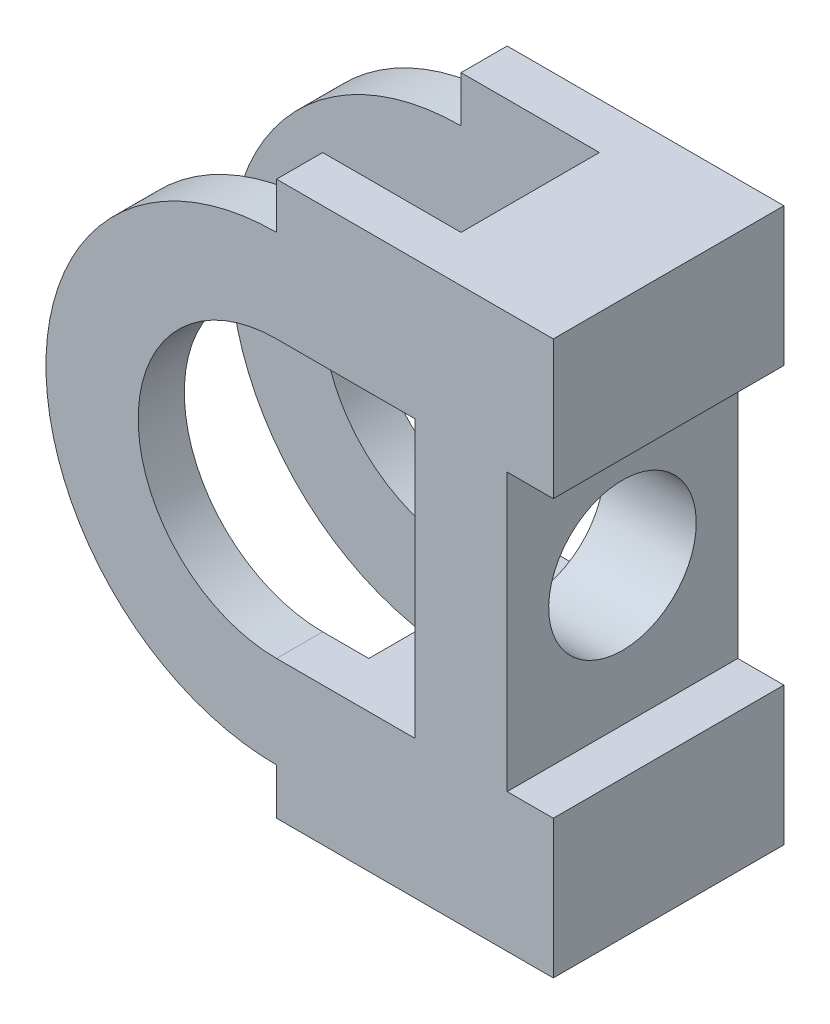
SolidWorks part; units mm, degrees
ref_plane "Front Plane" through (0, 0, 0) normal (0, 0, 1) x (1, 0, 0)
ref_plane "Top Plane" through (0, 0, 0) normal (0, 1, 0) x (1, 0, 0)
ref_plane "Right Plane" through (0, 0, 0) normal (1, 0, 0) x (0, 0, -1)
sketch "Sketch1" plane through (0, 0, 0) normal (0, 0, 1) x (1, 0, 0)
  line L0 (0, 120) -> (0, 110)
  line L1 (0, 0) -> (60, 0)
  line L2 (0, 0) -> (0, 10)
  line L3 (0, 120) -> (60, 120)
  line L4 (60, 0) -> (60, 120)
  arc A0 (0, 110) -> (0, 10) centre (0, 60) ccw
  dimension "D1" = 60
  dimension "D6" = 50
  dimension "D2" = 60
  dimension "D3" = 120
  dimension "D4" = 10
  dimension "D5" = 10
extrude "Boss-Extrude1" add sketch "Sketch1" along normal blind 50
sketch "Sketch2" plane through (0, 0, 50) normal (0, 0, 1) x (1, 0, 0)
  line L0 (60, 0) -> (60, 120) construction
  line L1 (60, 90) -> (50, 90)
  line L2 (60, 90) -> (60, 30)
  line L3 (60, 30) -> (50, 30)
  line L4 (50, 90) -> (50, 30)
  dimension "D1" = 10
  dimension "D2" = 60
  dimension "D3" = 30
extrude "Cut-Extrude1" cut sketch "Sketch2" against normal blind 50
sketch "Sketch3" plane through (0, 0, 50) normal (0, 0, 1) x (1, 0, 0)
  line L0 (30, 90) -> (30, 30)
  line L1 (0, 90) -> (30, 90)
  line L2 (0, 30) -> (30, 30)
  arc A0 (0, 90) -> (0, 30) centre (0, 60) ccw
  dimension "D1" = 60
  dimension "D2" = 0
  dimension "D3" = 20
  dimension "D4" = 30
extrude "Cut-Extrude2" cut sketch "Sketch3" against normal blind 50
ref_plane "Plane1" through (0, 120, 0) normal (0, 1, 0) x (1, 0, 0)
sketch "Sketch4" plane through (0, 120, 0) normal (0, 1, 0) x (1, 0, 0)
  line L0 (60, -50) -> (60, 0) construction
  line L1 (10, -10) -> (-50, -10)
  line L2 (10, -10) -> (10, -40)
  line L3 (10, -40) -> (-50, -40)
  line L4 (-50, -10) -> (-50, -40)
  point P4 (60, -25)
  dimension "D1" = 30
  dimension "D2" = 10
  dimension "D3" = 50
  dimension "D4" = 60
extrude "Cut-Extrude3" cut sketch "Sketch4" against normal blind 177
sketch "Sketch5" plane through (30, 0, 0) normal (-1, 0, 0) x (0, 0, 1)
  line L0 (50, 30) -> (50, 90) construction
  circle A0 centre (25, 60) radius 16
  point P2 (50, 60)
  dimension "D1" = 32
  dimension "D2" = 30
  dimension "D3" = 25
extrude "Cut-Extrude5" cut sketch "Sketch5" against normal blind 177
sketch "Sketch6" plane through (0, 120, 0) normal (0, 1, 0) x (1, 0, 0)
  line L1 (10, -10) -> (30, -10)
  line L2 (10, -10) -> (10, -40)
  line L3 (10, -40) -> (30, -40)
  line L4 (30, -10) -> (30, -40)
  dimension "D1" = 20
  dimension "D2" = 30
extrude "Cut-Extrude6" cut sketch "Sketch6" against normal blind 20
sketch "Sketch7" plane through (0, 0, 0) normal (0, -1, 0) x (1, 0, 0)
  line L1 (10, 10) -> (30, 10)
  line L2 (10, 10) -> (10, 40)
  line L3 (10, 40) -> (30, 40)
  line L4 (30, 10) -> (30, 40)
  dimension "D1" = 30
  dimension "D2" = 20
extrude "Cut-Extrude7" cut sketch "Sketch7" against normal blind 20
